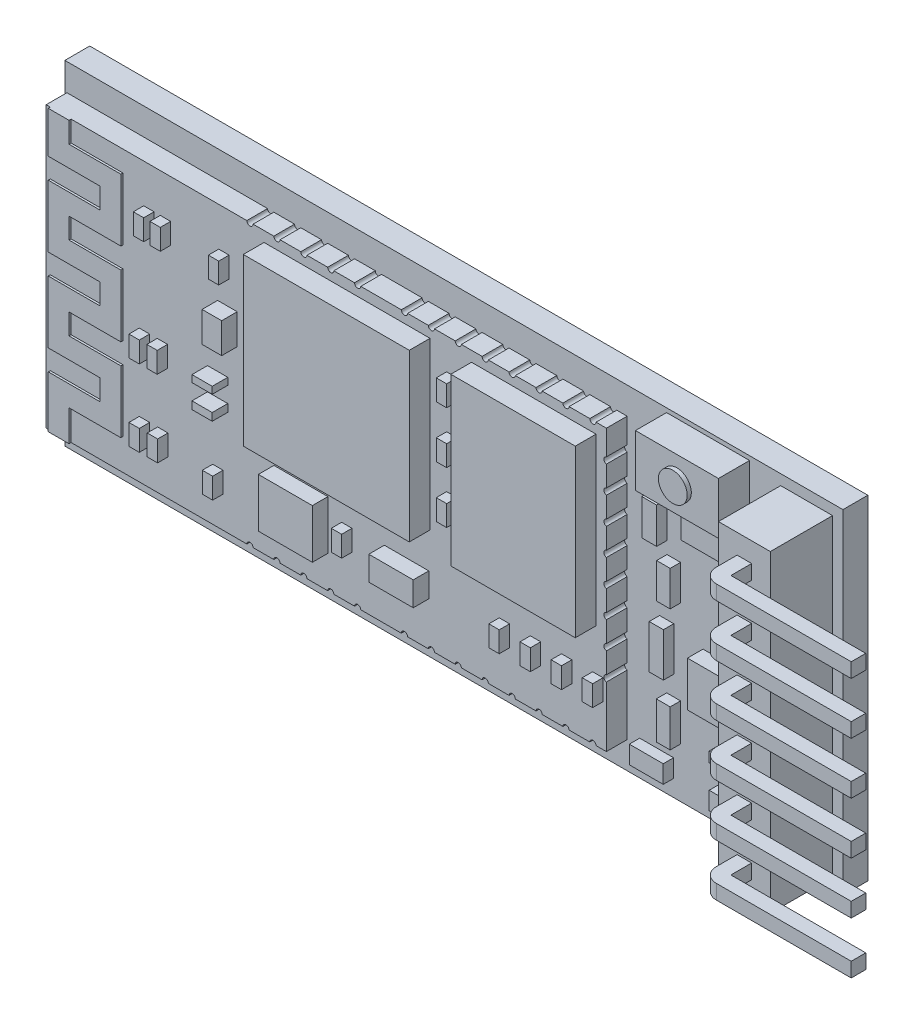
SolidWorks part; units mm, degrees
ref_plane "Ön Düzlem" through (0, 0, 0) normal (0, 0, 1) x (1, 0, 0)
ref_plane "Üst Düzlem" through (0, 0, 0) normal (0, 1, 0) x (1, 0, 0)
ref_plane "Sağ Düzlem" through (0, 0, 0) normal (1, 0, 0) x (0, 0, -1)
sketch "Çizim2" plane through (0, 0, 0) normal (0, 0, 1) x (1, 0, 0)
  line L1 (0, 0) -> (37.5, 0)
  line L2 (0, 0) -> (0, 16.1)
  line L3 (0, 16.1) -> (37.5, 16.1)
  line L4 (37.5, 0) -> (37.5, 16.1)
  dimension "D1" = 37.5
  dimension "D2" = 16.1
extrude "Yükseklik-Ekstrüzyon1" add sketch "Çizim2" along normal blind 1.2
sketch "Çizim5" plane through (0, 0, 1.2) normal (0, 0, 1) x (1, 0, 0)
  line L0 (37.5, 0) -> (37.5, 16.1) construction
  line L1 (34.5, 0.5) -> (37, 0.5)
  line L2 (34.5, 0.5) -> (34.5, 15.6)
  line L3 (34.5, 15.6) -> (37, 15.6)
  line L4 (37, 0.5) -> (37, 15.6)
  line L5 (0, 0) -> (37.5, 0) construction
  line L6 (37.5, 16.1) -> (0, 16.1) construction
  dimension "D1" = 0.5
  dimension "D2" = 0.5
  dimension "D3" = 0.5
  dimension "D4" = 2.5
extrude "Yükseklik-Ekstrüzyon2" add sketch "Çizim5" along normal blind 3
sketch "Çizim6" plane through (0, 0, 4.2) normal (0, 0, 1) x (1, 0, 0)
  line L0 (34.5, 3.05) -> (37, 3.05)
  line L1 (34.5, 15.6) -> (34.5, 0.5) construction
  line L3 (34.5, 5.55) -> (37, 5.55)
  line L4 (37, 0.5) -> (37, 15.6) construction
  line L5 (34.5, 8.05) -> (37, 8.05)
  line L6 (34.5, 10.55) -> (37, 10.55)
  line L7 (34.5, 15.6) -> (34.5, 0.5) construction
  line L8 (34.5, 13.05) -> (37, 13.05)
  line L9 (37, 0.5) -> (37, 15.6) construction
  line L10 (34.5, 0.55) -> (37, 0.55)
  line L11 (34.5, 15.55) -> (37, 15.55)
  line L12 (37, 15.6) -> (34.5, 15.6) construction
  line L13 (34.5, 0.5) -> (37, 0.5) construction
  line L14 (35.4, 4.65) -> (36.1, 4.65)
  line L15 (35.4, 2.15) -> (36.1, 2.15)
  line L16 (35.4, 2.15) -> (35.4, 1.45)
  line L17 (35.4, 1.45) -> (36.1, 1.45)
  line L18 (36.1, 2.15) -> (36.1, 1.45)
  line L19 (35.4, 4.65) -> (35.4, 3.95)
  line L20 (35.4, 3.95) -> (36.1, 3.95)
  line L21 (36.1, 4.65) -> (36.1, 3.95)
  line L22 (35.4, 7.15) -> (36.1, 7.15)
  line L23 (35.4, 7.15) -> (35.4, 6.45)
  line L24 (35.4, 6.45) -> (36.1, 6.45)
  line L25 (36.1, 7.15) -> (36.1, 6.45)
  line L26 (35.4, 12.15) -> (36.1, 12.15)
  line L27 (35.4, 12.15) -> (35.4, 11.45)
  line L28 (35.4, 11.45) -> (36.1, 11.45)
  line L29 (36.1, 12.15) -> (36.1, 11.45)
  line L30 (35.4, 9.65) -> (36.1, 9.65)
  line L31 (35.4, 9.65) -> (35.4, 8.95)
  line L32 (35.4, 8.95) -> (36.1, 8.95)
  line L33 (36.1, 9.65) -> (36.1, 8.95)
  line L34 (35.4, 14.65) -> (36.1, 14.65)
  line L35 (35.4, 14.65) -> (35.4, 13.95)
  line L36 (35.4, 13.95) -> (36.1, 13.95)
  line L37 (36.1, 14.65) -> (36.1, 13.95)
  dimension "D1" = 0.05
  dimension "D2" = 0.05
  dimension "D3" = 2.5
  dimension "D4" = 2.5
  dimension "D5" = 2.5
  dimension "D6" = 2.5
  dimension "D7" = 2.5
  dimension "D8" = 0.7
  dimension "D9" = 0.7
  dimension "D10" = 0.9
  dimension "D11" = 0.9
  dimension "D12" = 0.7
  dimension "D13" = 0.7
  dimension "D14" = 0.9
  dimension "D15" = 0.9
  dimension "D16" = 0.9
  dimension "D17" = 0.9
  dimension "D18" = 0.7
  dimension "D19" = 0.7
  dimension "D20" = 0.9
  dimension "D21" = 0.9
  dimension "D22" = 0.7
  dimension "D23" = 0.7
  dimension "D24" = 0.9
  dimension "D25" = 0.9
  dimension "D26" = 0.7
  dimension "D27" = 0.7
  dimension "D28" = 0.9
  dimension "D29" = 0.7
  dimension "D30" = 0.9
  dimension "D31" = 0.7
extrude "Yükseklik-Ekstrüzyon3" add sketch "Çizim6" along normal blind 1 separate body contours L18 L15 L16 L17 | L21 L14 L19 L20 | L33 L30 L31 L32 | L29 L26 L27 L28 | L37 L34 L35 L36 | L25 L24 L23 L22
sketch "Çizim8" plane through (0, 1.45, 0) normal (0, -1, 0) x (1, 0, 0)
  line L0 (36.1, 5.2) -> (42.6, 5.2)
  line L1 (42.6, 5.2) -> (42.6, 5.9)
  line L2 (42.6, 5.9) -> (36.1, 5.9)
  line L3 (35.4, 5.2) -> (36.1, 5.2)
  arc A0 (36.1, 5.9) -> (35.4, 5.2) centre (36.1, 5.2) ccw
  dimension "D2" = 0.7
  dimension "D1" = 0.7
  dimension "D3" = 6.5
extrude "Yükseklik-Ekstrüzyon4" add sketch "Çizim8" against normal blind 0.7
sketch "Çizim9" plane through (0, 3.95, 0) normal (0, -1, 0) x (1, 0, 0)
  line L0 (36.1, 5.2) -> (42.6, 5.2)
  line L1 (42.6, 5.2) -> (42.6, 5.9)
  line L2 (42.6, 5.9) -> (36.1, 5.9)
  line L3 (36.1, 5.2) -> (35.4, 5.2)
  line L4 (35.4, 5.2) -> (35.4, 4.2) construction
  line L5 (35.4, 5.2) -> (36.1, 5.2) construction
  arc A0 (35.4, 5.2) -> (36.1, 5.9) centre (36.1, 5.2) cw
  dimension "D1" = 6.5
  dimension "D2" = 0.7
  dimension "D3" = 6.5
extrude "Yükseklik-Ekstrüzyon5" add sketch "Çizim9" against normal blind 0.7
sketch "Çizim10" plane through (0, 6.45, 0) normal (0, -1, 0) x (1, 0, 0)
  line L0 (36.1, 5.2) -> (42.6, 5.2)
  line L1 (42.6, 5.2) -> (42.6, 5.9)
  line L2 (42.6, 5.9) -> (36.1, 5.9)
  line L3 (36.1, 5.2) -> (35.4, 5.2)
  arc A0 (35.4, 5.2) -> (36.1, 5.9) centre (36.1, 5.2) cw
extrude "Yükseklik-Ekstrüzyon6" add sketch "Çizim10" against normal blind 0.7
sketch "Çizim11" plane through (0, 8.95, 0) normal (0, -1, 0) x (1, 0, 0)
  line L0 (36.1, 5.2) -> (42.6, 5.2)
  line L1 (42.6, 5.2) -> (42.6, 5.9)
  line L2 (42.6, 5.9) -> (36.1, 5.9)
  line L3 (36.1, 5.2) -> (35.4, 5.2)
  arc A0 (35.4, 5.2) -> (36.1, 5.9) centre (36.1, 5.2) cw
extrude "Yükseklik-Ekstrüzyon7" add sketch "Çizim11" against normal blind 0.7
sketch "Çizim12" plane through (0, 11.45, 0) normal (0, -1, 0) x (1, 0, 0)
  line L0 (36.1, 5.2) -> (42.6, 5.2)
  line L1 (42.6, 5.2) -> (42.6, 5.9)
  line L2 (42.6, 5.9) -> (36.1, 5.9)
  line L3 (36.1, 5.2) -> (35.4, 5.2)
  arc A0 (35.4, 5.2) -> (36.1, 5.9) centre (36.1, 5.2) cw
extrude "Yükseklik-Ekstrüzyon8" add sketch "Çizim12" against normal blind 0.7
sketch "Çizim13" plane through (0, 13.95, 0) normal (0, -1, 0) x (1, 0, 0)
  line L0 (36.1, 5.2) -> (42.6, 5.2)
  line L1 (42.6, 5.2) -> (42.6, 5.9)
  line L2 (42.6, 5.9) -> (36.1, 5.9)
  line L3 (36.1, 5.2) -> (35.4, 5.2)
  arc A0 (35.4, 5.2) -> (36.1, 5.9) centre (36.1, 5.2) cw
extrude "Yükseklik-Ekstrüzyon9" add sketch "Çizim13" against normal blind 0.7
sketch "Çizim14" plane through (0, 0, 1.2) normal (0, 0, 1) x (1, 0, 0)
  line L1 (0.1, 14.8) -> (27.1, 14.8)
  line L2 (0.1, 14.8) -> (0.1, 1.3)
  line L3 (0.1, 1.3) -> (27.1, 1.3)
  line L4 (27.1, 14.8) -> (27.1, 1.3)
  line L5 (37.5, 16.1) -> (0, 16.1) construction
  line L7 (0, 16.1) -> (0, 0) construction
  point P6 (0, 8.05)
  dimension "D1" = 13.5
  dimension "D2" = 27
  dimension "D3" = 1.3
  dimension "D4" = 0.1
extrude "Yükseklik-Ekstrüzyon10" add sketch "Çizim14" along normal blind 1
sketch "Çizim15" plane through (0, 0, 2.2) normal (0, 0, 1) x (1, 0, 0)
  line L0 (0.3, 1.3) -> (0.3, 14.8) construction
  line L1 (0.1, 1.3) -> (27.1, 1.3) construction
  line L2 (27.1, 14.8) -> (0.1, 14.8) construction
  line L3 (0.1, 14.8) -> (0.1, 1.3) construction
  line L4 (3.8, 14.8) -> (3.8, 1.3) construction
  line L5 (0.3, 1.3) -> (0.3, 3.8)
  line L6 (1.3, 2.8) -> (3.8, 2.8)
  line L7 (3.8, 2.8) -> (3.8, 5.8)
  line L8 (0.3, 3.8) -> (2.8, 3.8)
  line L9 (1.3, 1.3) -> (1.3, 2.8)
  line L10 (0.1, 1.3) -> (27.1, 1.3) construction
  line L11 (2.8, 3.8) -> (2.8, 4.8)
  line L12 (2.8, 4.8) -> (0.3, 4.8)
  line L13 (0.3, 4.8) -> (0.3, 7.8)
  line L14 (0.3, 7.8) -> (2.8, 7.8)
  line L15 (3.8, 5.8) -> (1.3, 5.8)
  line L16 (1.3, 5.8) -> (1.3, 6.8)
  line L17 (1.3, 6.8) -> (3.8, 6.8)
  line L18 (3.8, 6.8) -> (3.8, 9.8)
  line L19 (2.8, 7.8) -> (2.8, 8.8)
  line L20 (2.8, 8.8) -> (0.3, 8.8)
  line L21 (0.3, 8.8) -> (0.3, 11.8)
  line L22 (3.8, 9.8) -> (1.3, 9.8)
  line L23 (1.3, 9.8) -> (1.3, 10.8)
  line L24 (1.3, 10.8) -> (3.8, 10.8)
  line L25 (3.8, 10.8) -> (3.8, 13.8)
  line L26 (0.3, 11.8) -> (2.8, 11.8)
  line L27 (2.8, 11.8) -> (2.8, 12.8)
  line L28 (2.8, 12.8) -> (0.3, 12.8)
  line L29 (0.3, 12.8) -> (0.3, 14.8)
  line L30 (3.8, 13.8) -> (1.3, 13.8)
  line L31 (1.3, 13.8) -> (1.3, 14.8)
  line L32 (1.3, 14.8) -> (0.3, 14.8)
  line L33 (1.3, 1.3) -> (0.3, 1.3)
  dimension "D1" = 0.2
  dimension "D2" = 3.5
  dimension "D3" = 2.5
  dimension "D4" = 1
  dimension "D5" = 1.5
  dimension "D6" = 3
  dimension "D7" = 1
  dimension "D8" = 1
  dimension "D9" = 1
  dimension "D10" = 1
  dimension "D11" = 1
  dimension "D12" = 2.5
  dimension "D13" = 3
  dimension "D14" = 2.5
  dimension "D15" = 3
  dimension "D16" = 1
  dimension "D17" = 1
  dimension "D18" = 1
  dimension "D19" = 2.5
  dimension "D20" = 2.5
  dimension "D21" = 1
  dimension "D22" = 3
  dimension "D23" = 1
extrude "Yükseklik-Ekstrüzyon11" add sketch "Çizim15" along normal blind 0.1
sketch "Çizim16" plane through (0, 0, 1.2) normal (0, 0, 1) x (1, 0, 0)
  line L0 (37.5, 16.1) -> (0, 16.1) construction
  line L1 (29, 15.9) -> (33, 15.9)
  line L2 (29, 15.9) -> (29, 13.4)
  line L3 (29, 13.4) -> (33, 13.4)
  line L4 (33, 15.9) -> (33, 13.4)
  line L5 (34.5, 15.6) -> (34.5, 0.5) construction
  dimension "D1" = 2.5
  dimension "D2" = 4
  dimension "D3" = 0.2
  dimension "D4" = 1.5
extrude "Yükseklik-Ekstrüzyon12" add sketch "Çizim16" along normal blind 1.5 separate body
sketch "Çizim17" plane through (0, 0, 2.7) normal (0, 0, 1) x (1, 0, 0)
  line L0 (29, 14.65) -> (33, 14.65) construction
  line L1 (29, 15.9) -> (29, 13.4) construction
  line L2 (33, 13.4) -> (33, 15.9) construction
  line L3 (31, 15.9) -> (31, 13.4) construction
  line L4 (33, 15.9) -> (29, 15.9) construction
  line L5 (29, 13.4) -> (33, 13.4) construction
  circle A0 centre (31, 14.65) radius 0.6936
extrude "Yükseklik-Ekstrüzyon13" add sketch "Çizim17" along normal blind 0.2
sketch "Çizim18" plane through (0, 0, 2.2) normal (0, 0, 1) x (1, 0, 0)
  line L0 (27.1, 14.8) -> (1.3, 14.8) construction
  line L1 (26.6004, 6.3) -> (20.6004, 6.3)
  line L2 (26.6004, 6.3) -> (26.6004, 14.3)
  line L3 (26.6004, 14.3) -> (20.6004, 14.3)
  line L4 (20.6004, 6.3) -> (20.6004, 14.3)
  line L5 (27.1, 1.3) -> (27.1, 14.8) construction
  line L7 (18.6004, 6.3) -> (10.6004, 6.3)
  line L8 (18.6004, 6.3) -> (18.6004, 14.3)
  line L9 (18.6004, 14.3) -> (10.6004, 14.3)
  line L10 (10.6004, 6.3) -> (10.6004, 14.3)
  dimension "D1" = 8
  dimension "D2" = 6
  dimension "D3" = 0.5
  dimension "D4" = 0.4996
  dimension "D5" = 2
  dimension "D6" = 8
  dimension "D7" = 8
  dimension "D8" = 0.5
extrude "Yükseklik-Ekstrüzyon14" add sketch "Çizim18" along normal blind 1
sketch "Çizim19" plane through (0, 0, 2.2) normal (0, 0, 1) x (1, 0, 0)
  line L0 (3.8, 10.8) -> (3.8, 13.8) construction
  line L1 (4.8, 11.93) -> (5.3, 11.93)
  line L2 (4.8, 11.93) -> (4.8, 12.93)
  line L3 (4.8, 12.93) -> (5.3, 12.93)
  line L4 (5.3, 11.93) -> (5.3, 12.93)
  line L5 (5.6, 11.93) -> (6.1, 11.93)
  line L6 (5.6, 11.93) -> (5.6, 12.93)
  line L7 (5.6, 12.93) -> (6.1, 12.93)
  line L8 (6.1, 11.93) -> (6.1, 12.93)
  line L9 (8.4157, 11.93) -> (8.9157, 11.93)
  line L10 (8.4157, 11.93) -> (8.4157, 12.93)
  line L11 (8.4157, 12.93) -> (8.9157, 12.93)
  line L12 (8.9157, 11.93) -> (8.9157, 12.93)
  dimension "D1" = 1
  dimension "D2" = 0.5
  dimension "D3" = 1
  dimension "D4" = 0.5
  dimension "D5" = 1
  dimension "D6" = 0.5
  dimension "D7" = 1
  dimension "D8" = 0.3
extrude "Yükseklik-Ekstrüzyon15" add sketch "Çizim19" along normal blind 0.5
sketch "Çizim22" plane through (0, 0, 2.2) normal (0, 0, 1) x (1, 0, 0)
  line L0 (4.589, 6.722) -> (5.089, 6.722)
  line L1 (4.589, 6.722) -> (4.589, 7.722)
  line L2 (4.589, 7.722) -> (5.089, 7.722)
  line L3 (5.089, 6.722) -> (5.089, 7.722)
  line L4 (5.4516, 6.722) -> (5.9516, 6.722)
  line L5 (5.4516, 6.722) -> (5.4516, 7.722)
  line L6 (5.4516, 7.722) -> (5.9516, 7.722)
  line L7 (5.9516, 6.722) -> (5.9516, 7.722)
  line L8 (4.5888, 3.0335) -> (5.0888, 3.0335)
  line L9 (4.5888, 3.0335) -> (4.5888, 4.0335)
  line L10 (4.5888, 4.0335) -> (5.0888, 4.0335)
  line L11 (5.0888, 3.0335) -> (5.0888, 4.0335)
  line L12 (5.4701, 3.0335) -> (5.9701, 3.0335)
  line L13 (5.4701, 3.0335) -> (5.4701, 4.0335)
  line L14 (5.4701, 4.0335) -> (5.9701, 4.0335)
  line L15 (5.9701, 3.0335) -> (5.9701, 4.0335)
  line L16 (8.1243, 2.8062) -> (8.6243, 2.8062)
  line L17 (8.1243, 2.8062) -> (8.1243, 3.8062)
  line L18 (8.1243, 3.8062) -> (8.6243, 3.8062)
  line L19 (8.6243, 2.8062) -> (8.6243, 3.8062)
  line L20 (19.4004, 12.3) -> (19.9004, 12.3)
  line L21 (19.4004, 12.3) -> (19.4004, 13.3)
  line L22 (19.4004, 13.3) -> (19.9004, 13.3)
  line L23 (19.9004, 12.3) -> (19.9004, 13.3)
  line L24 (19.4004, 9.8) -> (19.9004, 9.8)
  line L25 (19.4004, 9.8) -> (19.4004, 10.8)
  line L26 (19.4004, 10.8) -> (19.9004, 10.8)
  line L27 (19.9004, 9.8) -> (19.9004, 10.8)
  line L28 (19.9004, 7.3) -> (19.4004, 7.3)
  line L29 (19.9004, 7.3) -> (19.9004, 8.3)
  line L30 (19.9004, 8.3) -> (19.4004, 8.3)
  line L31 (19.4004, 7.3) -> (19.4004, 8.3)
  line L32 (26.4351, 3.3) -> (26.9351, 3.3)
  line L33 (26.4351, 3.3) -> (26.4351, 4.3)
  line L34 (26.4351, 4.3) -> (26.9351, 4.3)
  line L35 (26.9351, 3.3) -> (26.9351, 4.3)
  line L36 (24.9351, 3.3) -> (25.4351, 3.3)
  line L37 (24.9351, 3.3) -> (24.9351, 4.3)
  line L38 (24.9351, 4.3) -> (25.4351, 4.3)
  line L39 (25.4351, 3.3) -> (25.4351, 4.3)
  line L40 (23.4351, 3.3) -> (23.9351, 3.3)
  line L41 (23.4351, 3.3) -> (23.4351, 4.3)
  line L42 (23.4351, 4.3) -> (23.9351, 4.3)
  line L43 (23.9351, 3.3) -> (23.9351, 4.3)
  line L44 (21.9351, 3.3) -> (22.4351, 3.3)
  line L45 (21.9351, 3.3) -> (21.9351, 4.3)
  line L46 (21.9351, 4.3) -> (22.4351, 4.3)
  line L47 (22.4351, 3.3) -> (22.4351, 4.3)
  line L48 (14.3404, 3.4908) -> (14.8404, 3.4908)
  line L49 (14.3404, 3.4908) -> (14.3404, 4.4908)
  line L50 (14.3404, 4.4908) -> (14.8404, 4.4908)
  line L51 (14.8404, 3.4908) -> (14.8404, 4.4908)
  line L52 (27.1, 14.8) -> (1.3, 14.8) construction
  line L54 (20.6004, 14.3) -> (20.6004, 6.3) construction
  line L55 (20.6004, 6.3) -> (26.6004, 6.3) construction
  dimension "D1" = 1
  dimension "D2" = 1
  dimension "D3" = 1
  dimension "D4" = 1
  dimension "D5" = 1
  dimension "D6" = 1
  dimension "D7" = 1
  dimension "D8" = 1
  dimension "D9" = 1
  dimension "D10" = 1
  dimension "D11" = 1
  dimension "D12" = 1
  dimension "D13" = 1
  dimension "D14" = 0.5
  dimension "D15" = 0.5
  dimension "D16" = 0.5
  dimension "D17" = 1.5
  dimension "D18" = 1.5
  dimension "D19" = 1.5
  dimension "D20" = 0.7
  dimension "D21" = 2
  dimension "D22" = 1
  dimension "D23" = 1
  dimension "D24" = 1
  dimension "D25" = 0.5
  dimension "D26" = 0.5
  dimension "D27" = 0.5
  dimension "D28" = 0.5
extrude "Yükseklik-Ekstrüzyon17" add sketch "Çizim22" along normal blind 0.5
sketch "Çizim23" plane through (0, 0, 2.2) normal (0, 0, 1) x (1, 0, 0)
  line L1 (11.0751, 2.8642) -> (13.6775, 2.8642)
  line L2 (11.0751, 2.8642) -> (11.0751, 5.2317)
  line L3 (11.0751, 5.2317) -> (13.6775, 5.2317)
  line L4 (13.6775, 2.8642) -> (13.6775, 5.2317)
  line L6 (16.3989, 3.3962) -> (18.5402, 3.3962)
  line L7 (16.3989, 3.3962) -> (16.3989, 4.5627)
  line L8 (16.3989, 4.5627) -> (18.5402, 4.5627)
  line L9 (18.5402, 3.3962) -> (18.5402, 4.5627)
  line L10 (7.8761, 6.3372) -> (8.8522, 6.3372)
  line L11 (7.8761, 6.3372) -> (7.8761, 6.7031)
  line L12 (7.8761, 6.7031) -> (8.8522, 6.7031)
  line L13 (8.8522, 6.3372) -> (8.8522, 6.7031)
  line L14 (7.8761, 7.4637) -> (8.8522, 7.4637)
  line L15 (7.8761, 7.4637) -> (7.8761, 7.7984)
  line L16 (7.8761, 7.7984) -> (8.8522, 7.7984)
  line L17 (8.8522, 7.4637) -> (8.8522, 7.7984)
  line L18 (8.3641, 9.3029) -> (9.3075, 9.3029)
  line L19 (8.3641, 9.3029) -> (8.3641, 10.7632)
  line L20 (8.3641, 10.7632) -> (9.3075, 10.7632)
  line L21 (9.3075, 9.3029) -> (9.3075, 10.7632)
extrude "Yükseklik-Ekstrüzyon18" add sketch "Çizim23" along normal blind 0.75
sketch "Çizim24" plane through (0, 0, 1.2) normal (0, 0, 1) x (1, 0, 0)
  line L1 (30.2001, 11.4276) -> (32.9069, 11.4276)
  line L2 (30.2001, 11.4276) -> (30.2001, 13.1705)
  line L3 (30.2001, 13.1705) -> (32.9069, 13.1705)
  line L4 (32.9069, 11.4276) -> (32.9069, 13.1705)
  line L5 (28.3044, 10.5724) -> (29.0208, 10.5724)
  line L6 (28.3044, 10.5724) -> (28.3044, 12.2991)
  line L7 (28.3044, 12.2991) -> (29.0208, 12.2991)
  line L8 (29.0208, 10.5724) -> (29.0208, 12.2991)
  line L9 (29.0208, 8.2903) -> (29.6736, 8.2903)
  line L10 (29.0208, 8.2903) -> (29.0208, 9.9841)
  line L11 (29.0208, 9.9841) -> (29.6736, 9.9841)
  line L12 (29.6736, 8.2903) -> (29.6736, 9.9841)
  line L13 (28.6626, 5.1548) -> (29.3472, 5.1548)
  line L14 (28.6626, 5.1548) -> (28.6626, 7.2612)
  line L15 (28.6626, 7.2612) -> (29.3472, 7.2612)
  line L16 (29.3472, 5.1548) -> (29.3472, 7.2612)
  line L17 (29.0049, 2.403) -> (29.6736, 2.403)
  line L18 (29.0049, 2.403) -> (29.0049, 4.2038)
  line L19 (29.0049, 4.2038) -> (29.6736, 4.2038)
  line L20 (29.6736, 2.403) -> (29.6736, 4.2038)
  line L21 (27.7053, 0.8007) -> (29.3393, 0.8007)
  line L22 (27.7053, 0.8007) -> (27.7053, 1.6631)
  line L23 (27.7053, 1.6631) -> (29.3393, 1.6631)
  line L24 (29.3393, 0.8007) -> (29.3393, 1.6631)
  line L25 (31.5535, 0.8007) -> (32.9069, 0.8007)
  line L26 (31.5535, 0.8007) -> (31.5535, 1.6631)
  line L27 (31.5535, 1.6631) -> (32.9069, 1.6631)
  line L28 (32.9069, 0.8007) -> (32.9069, 1.6631)
  line L29 (31.5535, 2.804) -> (32.9069, 2.804)
  line L30 (31.5535, 2.804) -> (31.5535, 3.3034)
  line L31 (31.5535, 3.3034) -> (32.9069, 3.3034)
  line L32 (32.9069, 2.804) -> (32.9069, 3.3034)
  line L33 (32.0202, 10.8077) -> (33.3885, 10.8077)
  line L34 (32.0202, 10.8077) -> (32.0202, 9.9841)
  line L35 (32.0202, 9.9841) -> (33.3885, 9.9841)
  line L36 (33.3885, 10.8077) -> (33.3885, 9.9841)
  line L37 (32.0202, 8.2903) -> (33.3885, 8.2903)
  line L38 (32.0202, 8.2903) -> (32.0202, 9.082)
  line L39 (32.0202, 9.082) -> (33.3885, 9.082)
  line L40 (33.3885, 8.2903) -> (33.3885, 9.082)
extrude "Yükseklik-Ekstrüzyon19" add sketch "Çizim24" along normal blind 0.5
sketch "Çizim25" plane through (0, 0, 1.2) normal (0, 0, 1) x (1, 0, 0)
  line L1 (30.7569, 4.7405) -> (33.8081, 4.7405)
  line L2 (30.7569, 4.7405) -> (30.7569, 6.9062)
  line L3 (30.7569, 6.9062) -> (33.8081, 6.9062)
  line L4 (33.8081, 4.7405) -> (33.8081, 6.9062)
extrude "Yükseklik-Ekstrüzyon20" add sketch "Çizim25" along normal blind 0.75
sketch "Çizim27" plane through (0, 0, 2.2) normal (0, 0, 1) x (1, 0, 0)
  line L0 (27.1, 14.8) -> (1.3, 14.8) construction
  line L1 (27.1, 1.3) -> (27.1, 14.8) construction
  line L2 (26.6, 14.8) -> (26.3, 14.8)
  line L3 (25.3, 14.8) -> (25.0045, 14.8)
  line L4 (24.5045, 14.4582) -> (24.5045, 15.2412) construction
  line L5 (23.7089, 14.8) -> (24.0045, 14.8)
  line L6 (22.4089, 14.8) -> (22.7089, 14.8)
  line L7 (21.9089, 14.5317) -> (21.9089, 15.1738) construction
  line L8 (21.4089, 14.8) -> (21.1089, 14.8)
  line L9 (20.1089, 14.8) -> (19.8134, 14.8)
  line L10 (18.5179, 14.8) -> (18.8134, 14.8)
  line L11 (17.2179, 14.8) -> (17.5179, 14.8)
  line L12 (16.2399, 14.5317) -> (16.2399, 15.1738) construction
  line L13 (10.5708, 14.5317) -> (10.5708, 15.1738) construction
  line L14 (15.2619, 14.8) -> (14.9619, 14.8)
  line L15 (13.9619, 14.8) -> (13.6663, 14.8)
  line L16 (12.3708, 14.8) -> (12.6663, 14.8)
  line L17 (11.0708, 14.8) -> (11.3708, 14.8)
  line L18 (10.0708, 14.8) -> (9.7708, 14.8)
  line L19 (27.1, 8.05) -> (0.1, 8.05) construction
  line L20 (0.1, 14.8) -> (0.1, 1.3) construction
  line L21 (10.5708, 1.5683) -> (10.5708, 0.9262) construction
  line L22 (16.2399, 1.5683) -> (16.2399, 0.9262) construction
  line L23 (21.9089, 1.5683) -> (21.9089, 0.9262) construction
  line L24 (24.5045, 1.6418) -> (24.5045, 0.8588) construction
  line L25 (10.0708, 1.3) -> (9.7708, 1.3)
  line L26 (11.0708, 1.3) -> (11.3708, 1.3)
  line L27 (12.3708, 1.3) -> (12.6663, 1.3)
  line L28 (13.9619, 1.3) -> (13.6663, 1.3)
  line L29 (15.2619, 1.3) -> (14.9619, 1.3)
  line L30 (17.2179, 1.3) -> (17.5179, 1.3)
  line L31 (18.5179, 1.3) -> (18.8134, 1.3)
  line L32 (20.1089, 1.3) -> (19.8134, 1.3)
  line L33 (21.4089, 1.3) -> (21.1089, 1.3)
  line L34 (22.4089, 1.3) -> (22.7089, 1.3)
  line L35 (23.7089, 1.3) -> (24.0045, 1.3)
  line L36 (25.3, 1.3) -> (25.0045, 1.3)
  line L37 (26.6, 1.3) -> (26.3, 1.3)
  arc A0 (26.6, 14.8) -> (26.3, 14.8) centre (26.45, 14.8) cw
  arc A1 (25.3, 14.8) -> (25.0045, 14.8) centre (25.1522, 14.8) cw
  arc A2 (23.7089, 14.8) -> (24.0045, 14.8) centre (23.8567, 14.8) ccw
  arc A3 (22.4089, 14.8) -> (22.7089, 14.8) centre (22.5589, 14.8) ccw
  arc A4 (21.4089, 14.8) -> (21.1089, 14.8) centre (21.2589, 14.8) cw
  arc A5 (20.1089, 14.8) -> (19.8134, 14.8) centre (19.9612, 14.8) cw
  arc A6 (18.5179, 14.8) -> (18.8134, 14.8) centre (18.6656, 14.8) ccw
  arc A7 (17.2179, 14.8) -> (17.5179, 14.8) centre (17.3679, 14.8) ccw
  arc A8 (15.2619, 14.8) -> (14.9619, 14.8) centre (15.1119, 14.8) cw
  arc A9 (13.9619, 14.8) -> (13.6663, 14.8) centre (13.8141, 14.8) cw
  arc A10 (12.3708, 14.8) -> (12.6663, 14.8) centre (12.5186, 14.8) ccw
  arc A11 (11.0708, 14.8) -> (11.3708, 14.8) centre (11.2208, 14.8) ccw
  arc A12 (10.0708, 14.8) -> (9.7708, 14.8) centre (9.9208, 14.8) cw
  arc A13 (10.0708, 1.3) -> (9.7708, 1.3) centre (9.9208, 1.3) ccw
  arc A14 (11.0708, 1.3) -> (11.3708, 1.3) centre (11.2208, 1.3) cw
  arc A15 (12.3708, 1.3) -> (12.6663, 1.3) centre (12.5186, 1.3) cw
  arc A16 (13.9619, 1.3) -> (13.6663, 1.3) centre (13.8141, 1.3) ccw
  arc A17 (15.2619, 1.3) -> (14.9619, 1.3) centre (15.1119, 1.3) ccw
  arc A18 (17.2179, 1.3) -> (17.5179, 1.3) centre (17.3679, 1.3) cw
  arc A19 (18.5179, 1.3) -> (18.8134, 1.3) centre (18.6656, 1.3) cw
  arc A20 (20.1089, 1.3) -> (19.8134, 1.3) centre (19.9612, 1.3) ccw
  arc A21 (21.4089, 1.3) -> (21.1089, 1.3) centre (21.2589, 1.3) ccw
  arc A22 (22.4089, 1.3) -> (22.7089, 1.3) centre (22.5589, 1.3) cw
  arc A23 (23.7089, 1.3) -> (24.0045, 1.3) centre (23.8567, 1.3) cw
  arc A24 (25.3, 1.3) -> (25.0045, 1.3) centre (25.1522, 1.3) ccw
  arc A25 (26.6, 1.3) -> (26.3, 1.3) centre (26.45, 1.3) ccw
  dimension "D1" = 0.5
  dimension "D2" = 0.3
  dimension "D3" = 1
  dimension "D4" = 0.5
  dimension "D5" = 0.5
extrude "Kes-Ekstrüzyon1" cut sketch "Çizim27" against normal blind 1
sketch "Çizim28" plane through (0, 0, 2.2) normal (0, 0, 1) x (1, 0, 0)
  line L0 (27.1, 1.3) -> (27.1, 14.8) construction
  line L1 (27.1, 13.3005) -> (27.1, 13.5998)
  line L2 (26.7694, 12.8005) -> (27.3012, 12.8005) construction
  line L3 (27.1, 12.3005) -> (27.1, 12.0011)
  line L4 (26.8075, 11.5011) -> (27.3621, 11.5011) construction
  line L5 (27.1, 10.7018) -> (27.1, 11.0011)
  line L6 (27.1, 9.7018) -> (27.1, 9.4024)
  line L7 (26.7694, 8.9024) -> (27.3621, 8.9024) construction
  line L8 (27.3621, 8.9024) -> (27.0657, 8.9024) construction
  line L9 (26.8075, 6.3037) -> (27.3621, 6.3037) construction
  line L10 (26.7694, 5.0044) -> (27.3012, 5.0044) construction
  line L11 (27.1, 8.1031) -> (27.1, 8.4024)
  line L12 (27.1, 7.1031) -> (27.1, 6.8037)
  line L13 (27.1, 5.5044) -> (27.1, 5.8037)
  line L14 (27.1, 4.5044) -> (27.1, 4.205)
  arc A0 (27.1, 13.5998) -> (27.1, 13.3005) centre (27.1317, 13.4502) ccw
  arc A1 (27.1, 12.0011) -> (27.1, 12.3005) centre (27.1317, 12.1508) cw
  arc A2 (27.1, 11.0011) -> (27.1, 10.7018) centre (27.1317, 10.8514) ccw
  arc A3 (27.1, 9.4024) -> (27.1, 9.7018) centre (27.1317, 9.5521) cw
  arc A4 (27.1, 8.4024) -> (27.1, 8.1031) centre (27.1317, 8.2527) ccw
  arc A5 (27.1, 6.8037) -> (27.1, 7.1031) centre (27.1317, 6.9534) cw
  arc A6 (27.1, 5.8037) -> (27.1, 5.5044) centre (27.1317, 5.654) ccw
  arc A7 (27.1, 4.205) -> (27.1, 4.5044) centre (27.1317, 4.3547) cw
  dimension "D1" = 0.5
  dimension "D2" = 0.5
  dimension "D3" = 0.5
extrude "Kes-Ekstrüzyon2" cut sketch "Çizim28" against normal blind 1
